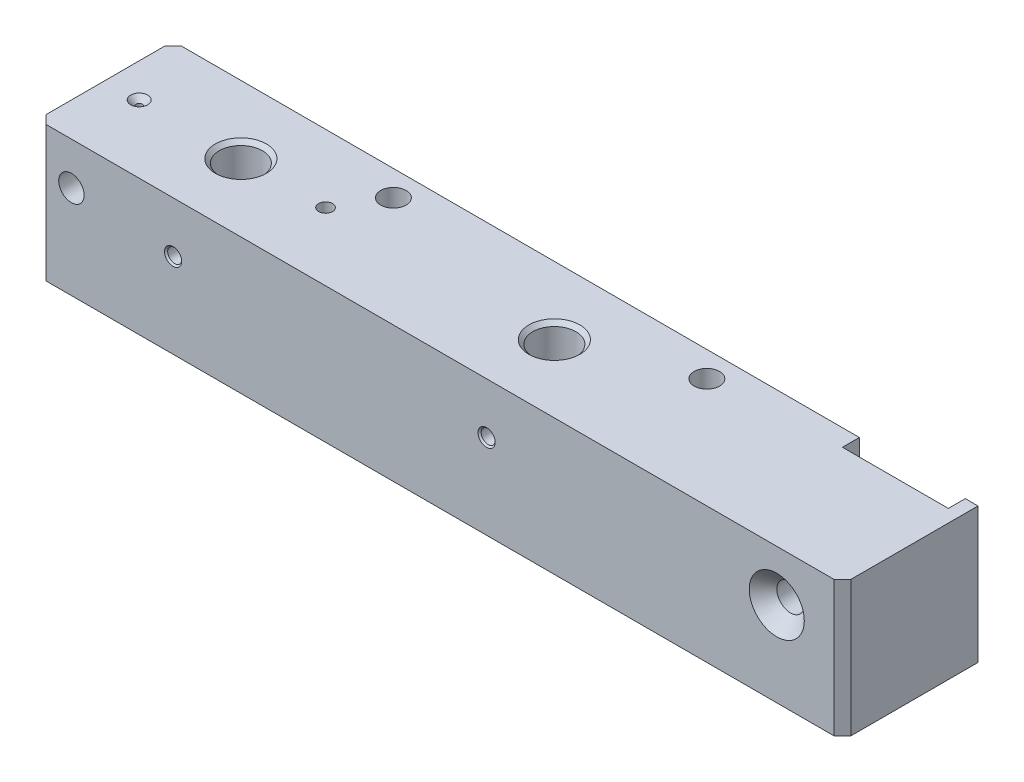
SolidWorks part; units mm, degrees
ref_plane "Front Plane" through (0, 0, 0) normal (0, 0, 1) x (1, 0, 0)
ref_plane "Top Plane" through (0, 0, 0) normal (0, 1, 0) x (1, 0, 0)
ref_plane "Right Plane" through (0, 0, 0) normal (1, 0, 0) x (0, 0, -1)
sketch "Sketch1" plane through (0, 0, 0) normal (0, 0, 1) x (1, 0, 0)
  line L1 (-95, 16) -> (95, 16)
  line L2 (-95, 16) -> (-95, -16)
  line L3 (-95, -16) -> (95, -16)
  line L4 (95, 16) -> (95, -16)
  line L5 (-95, 16) -> (95, -16) construction
  line L6 (-95, -16) -> (95, 16) construction
  point P0 (0, 0)
  dimension "D1" = 190
  dimension "D2" = 32
extrude "Boss-Extrude1" add sketch "Sketch1" along normal mid plane 32
chamfer "Chamfer1" distance 2 angle 45 3 edges at (-95, 0, -16) (95, 0, 16) (-95, 0, 16)
sketch "Sketch3" plane through (0, 16, 0) normal (0, 1, 0) x (1, 0, 0)
  line L0 (95, 16) -> (-93, 16) construction
  line L1 (92, 16) -> (67, 16)
  line L2 (92, 16) -> (92, 12)
  line L3 (92, 12) -> (67, 12)
  line L4 (67, 16) -> (67, 12)
  line L5 (95, -14) -> (95, 16) construction
  dimension "D1" = 25
  dimension "D2" = 4
  dimension "D3" = 3
extrude "Cut-Extrude1" cut sketch "Sketch3" against normal through all
sketch "Sketch4" plane through (0, 16, 0) normal (0, 1, 0) x (1, 0, 0)
  line L0 (-95, 0) -> (95, 0) construction
  line L3 (95, -14) -> (95, 16) construction
  line L4 (11, 16) -> (11, -16) construction
  line L5 (67, 16) -> (-93, 16) construction
  line L6 (93, -16) -> (-93, -16) construction
  line L7 (-63, 16) -> (-63, -16) construction
  line L8 (67, 16) -> (67, 12) construction
  point P5 (0, 0)
  dimension "D1" = 56
  dimension "D2" = 74
hole_wizard "M12 Tapped Hole2" positions "Sketch8" profile "Sketch9" tap size "M12" standard "ISO"
sketch "Sketch8" plane through (0, 16, 0) normal (0, 1, 0) x (1, 0, 0)
  line L0 (-63, 16) -> (-63, -16) construction
  line L1 (11, 16) -> (11, -16) construction
  point P0 (-63, 0)
  point P4 (11, 0)
sketch "Sketch9" plane through (-63, 16, 0) normal (1, 0, 0) x (0, 0, 1)
  line L0 (0, 0) -> (0, 27.0644)
  line L1 (0, 27.0644) -> (5.1, 24)
  line L2 (5.1, 24) -> (5.1, 0.925)
  line L3 (5.1, 0.925) -> (6.025, 0)
  line L5 (6.025, 0) -> (0, 0)
  line L6 (-5.1, 0.925) -> (-6.025, 0) construction
  line L10 (0, 27.0644) -> (-5.1, 24) construction
  line L11 (0, -6.35) -> (0, 107.95) construction
  dimension "Tap Drill Dia." = 10.2
  dimension "Tap Drill Depth" = 24
  dimension "Near C'Sink Dia." = 12.05
  dimension "Near C'Sink Angle" = 90
  dimension "Drill Angle" = 118
cosmetic thread "Hole Thread3" parameters "D1"=24, "D2"=12
cosmetic thread "Hole Thread4" parameters "D1"=24, "D2"=12
sketch "Sketch10" plane through (0, 0, 16) normal (0, 0, 1) x (1, 0, 0)
  line L0 (-63, -8) -> (-63, 16) construction
  line L1 (-57.9, -8) -> (-68.1, -8) construction
  line L2 (-95, 16) -> (95, 16) construction
  line L3 (11, -8) -> (11, 16) construction
  line L4 (16.1, -8) -> (5.9, -8) construction
  line L5 (-63, 4) -> (11, 4) construction
hole_wizard "M4 Tapped Hole1" positions "Sketch13" profile "Sketch14" tap size "M4" standard "ISO"
sketch "Sketch13" plane through (0, 0, 16) normal (0, 0, 1) x (1, 0, 0)
  point P0 (-63, 4)
  point P3 (11, 4)
sketch "Sketch14" plane through (-63, 4, 16) normal (1, 0, 0) x (0, -1, 0)
  line L0 (0, 0) -> (0, 12.4914)
  line L1 (0, 12.4914) -> (1.65, 11.5)
  line L2 (1.65, 11.5) -> (1.65, 0.375)
  line L3 (1.65, 0.375) -> (2.025, 0)
  line L5 (2.025, 0) -> (0, 0)
  line L6 (-1.65, 0.375) -> (-2.025, 0) construction
  line L10 (0, 12.4914) -> (-1.65, 11.5) construction
  line L11 (0, -6.35) -> (0, 107.95) construction
  dimension "Tap Drill Dia." = 3.3
  dimension "Tap Drill Depth" = 11.5
  dimension "Near C'Sink Dia." = 4.05
  dimension "Near C'Sink Angle" = 90
  dimension "Drill Angle" = 118
cosmetic thread "Hole Thread5" parameters "D1"=8, "D2"=4
cosmetic thread "Hole Thread6" parameters "D1"=8, "D2"=4
sketch "Sketch15" plane through (0, 0, 16) normal (0, 0, 1) x (1, 0, 0)
  line L0 (93, 4) -> (77.5, 4) construction
  line L1 (93, -16) -> (93, 16) construction
  line L2 (77.5, 4) -> (77.5, -16) construction
  line L3 (-93, -16) -> (93, -16) construction
  dimension "D1" = 15.5
  dimension "D2" = 20
sketch "Sketch18" plane through (0, 0, 16) normal (0, 0, 1) x (1, 0, 0)
  line L0 (-63, 4) -> (-87, 4) construction
  line L1 (-87, 4) -> (-87, 17.9897) construction
  line L2 (-93, -16) -> (93, -16) construction
  circle A0 centre (-87, 6) radius 3
  dimension "D3" = 6
  dimension "D1" = 24
  dimension "D2" = 22
extrude "Cut-Extrude2" cut sketch "Sketch18" against normal through all
hole_wizard "CSK for M4 Countersunk Flat Head Screw1" positions "Sketch19" profile "Sketch20" countersink size "M4" standard "ISO"
sketch "Sketch19" plane through (0, 16, 0) normal (0, 1, 0) x (1, 0, 0)
  line L0 (-95, 0) -> (95, 0) construction
  point P0 (-87, 0)
  dimension "D1" = 24
sketch "Sketch20" plane through (-87, 16, 0) normal (1, 0, 0) x (0, 0, 1)
  line L0 (0, 0) -> (0, 10.4506)
  line L1 (0, 10.4506) -> (0.75, 10)
  line L2 (0.75, 10) -> (0.75, 1.25)
  line L3 (0.75, 1.25) -> (2, 0)
  line L5 (2, 0) -> (0, 0)
  line L6 (-0.75, 1.25) -> (-2, 0) construction
  line L10 (0, 10.4506) -> (-0.75, 10) construction
  line L11 (0, -6.35) -> (0, 107.95) construction
  dimension "Hole Dia." = 1.5
  dimension "Hole Depth" = 10
  dimension "Near C'Sink Dia." = 4
  dimension "Near C'Sink Angle" = 90
  dimension "Drill Angle" = 118
hole_wizard "M4 Tapped Hole3" positions "Sketch23" profile "Sketch24" tap size "M4" standard "ISO"
sketch "Sketch23" plane through (0, 16, 0) normal (0, 1, 0) x (1, 0, 0)
  line L0 (-95, 0) -> (95, 0) construction
  point P0 (-43, 0)
  dimension "D1" = 20
sketch "Sketch24" plane through (-43, 16, 0) normal (1, 0, 0) x (0, 0, 1)
  line L0 (0, 0) -> (0, 16.9914)
  line L1 (0, 16.9914) -> (1.65, 16)
  line L2 (1.65, 16) -> (1.65, 0)
  line L5 (1.65, 0) -> (0, 0)
  line L10 (0, 16.9914) -> (-1.65, 16) construction
  line L11 (0, -6.35) -> (0, 107.95) construction
  dimension "Tap Drill Dia." = 3.3
  dimension "Tap Drill Depth" = 16
  dimension "Drill Angle" = 118
cosmetic thread "Hole Thread8" parameters "D1"=8, "D2"=4
sketch "Sketch25" plane through (0, 16, 0) normal (0, 1, 0) x (1, 0, 0)
  line L0 (67, 16) -> (-93, 16) construction
  line L1 (-95, -14) -> (-95, 14) construction
  circle A0 centre (-37, 10) radius 3
  circle A1 centre (37, 10) radius 3
  dimension "D3" = 6
  dimension "D1" = 74
  dimension "D2" = 6
  dimension "D4" = 58
extrude "Cut-Extrude3" cut sketch "Sketch25" against normal through all
hole_wizard "CSK for M10 Countersunk Flat Head Screw1" positions "Sketch26" profile "Sketch27" countersink size "M10" standard "ISO" end condition through all
sketch "Sketch26" plane through (0, 0, 16) normal (0, 0, 1) x (1, 0, 0)
  line L0 (-93, -16) -> (93, -16) construction
  line L1 (95, 16) -> (95, -16) construction
  point P0 (79.5, 4)
  dimension "D1" = 20
  dimension "D2" = 15.5
sketch "Sketch27" plane through (79.5, 4, 16) normal (1, 0, 0) x (0, -1, 0)
  line L0 (0, 0) -> (0, 32)
  line L1 (0, 32) -> (3.25, 32)
  line L2 (3.25, 32) -> (3.25, 3.25)
  line L3 (3.25, 3.25) -> (6.5, 0)
  line L5 (6.5, 0) -> (0, 0)
  line L6 (-3.25, 3.25) -> (-6.5, 0) construction
  line L11 (0, -6.35) -> (0, 107.95) construction
  dimension "Thru Hole Dia." = 6.5
  dimension "Thru Hole Depth" = 32
  dimension "Near C'Sink Dia." = 13
  dimension "Near C'Sink Angle" = 90
